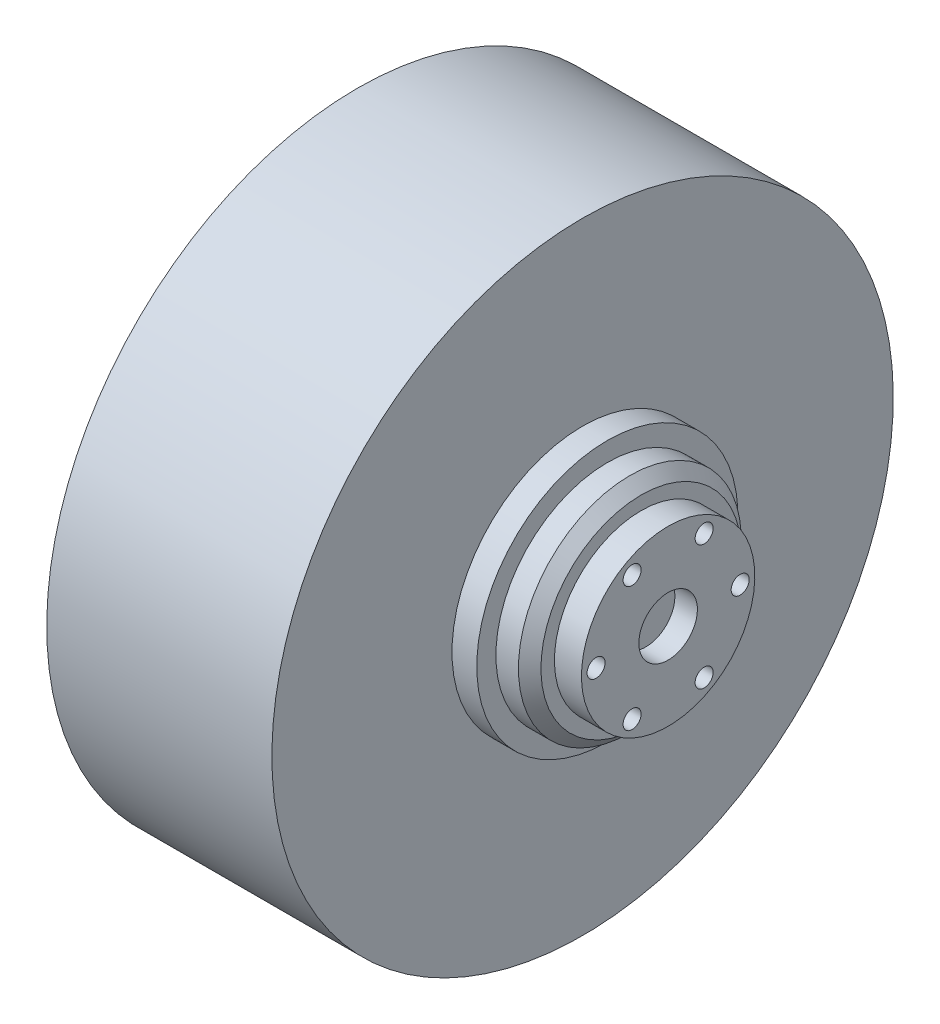
SolidWorks part; units mm, degrees
ref_plane "Płaszczyzna przednia" through (0, 0, 0) normal (0, 0, 1) x (1, 0, 0)
ref_plane "Płaszczyzna górna" through (0, 0, 0) normal (0, 1, 0) x (1, 0, 0)
ref_plane "Płaszczyzna prawa" through (0, 0, 0) normal (1, 0, 0) x (0, 0, -1)
sketch "Szkic1" plane through (0, 0, 0) normal (0, 0, 1) x (1, 0, 0)
  line L0 (-90, -36.5) -> (-70, -36.5)
  line L1 (-70, -36.5) -> (-70, -47)
  line L2 (-70, -47) -> (-48, -47)
  line L3 (-48, -47) -> (-48, -138)
  line L4 (-48, -138) -> (52, -138)
  line L5 (52, -138) -> (52, -58)
  line L6 (52, -58) -> (63, -58)
  line L7 (63, -58) -> (63, -49.5)
  line L8 (63, -49.5) -> (73, -49.5)
  line L9 (78, -44.5) -> (78, -38.5)
  line L10 (78, -38.5) -> (90, -38.5)
  line L11 (90, -38.5) -> (90, 0)
  line L12 (90, 0) -> (-90, 0)
  line L13 (-90, 0) -> (-90, -36.5)
  line L14 (73, -49.5) -> (78, -44.5)
  point P9 (78, -49.5)
  point P15 (90, -19.25)
  point P19 (0, 0)
  dimension "D1" = 180
  dimension "D2" = 36.5
  dimension "D3" = 47
  dimension "D4" = 22
  dimension "D5" = 100
  dimension "D6" = 12
  dimension "D7" = 38.5
  dimension "D8" = 138
  dimension "D9" = 26
  dimension "D10" = 58
  dimension "D11" = 10
  dimension "D13" = 6
revolve "Obrót1" add sketch "Szkic1" angle 360 about L12
sketch "Szkic4" plane through (90, 0, 0) normal (1, 0, 0) x (0, 0, -1)
  line L0 (0, 0) -> (22.2898, 0) construction
  circle A0 centre (16, 27.7128) radius 4
  circle A1 centre (32, 0) radius 4
  circle A2 centre (16, -27.7128) radius 4
  circle A3 centre (-16, -27.7128) radius 4
  circle A4 centre (-32, 0) radius 4
  circle A5 centre (-16, 27.7128) radius 4
  point P16 (0, 0)
  dimension "D1" = 8
  dimension "D2" = 32
  dimension "D3" = 6
extrude "Wytnij-wyciągnięcie1" cut sketch "Szkic4" against normal blind 10
sketch "Szkic5" plane through (90, 0, 0) normal (1, 0, 0) x (0, 0, -1)
  circle A0 centre (0, 0) radius 13
  dimension "D1" = 26
extrude "Wytnij-wyciągnięcie2" cut sketch "Szkic5" against normal blind 10 contours A0
